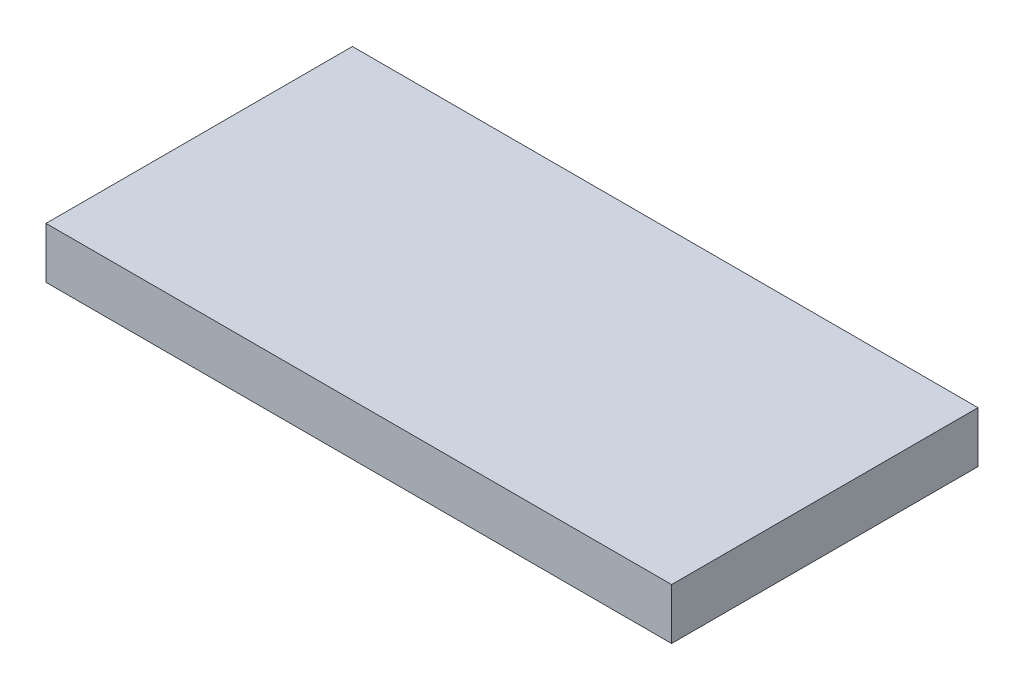
SolidWorks part; units mm, degrees
ref_plane "Front Plane" through (0, 0, 0) normal (0, 0, 1) x (1, 0, 0)
ref_plane "Top Plane" through (0, 0, 0) normal (0, 1, 0) x (1, 0, 0)
ref_plane "Right Plane" through (0, 0, 0) normal (1, 0, 0) x (0, 0, -1)
sketch "Sketch1" plane through (0, 0, 0) normal (0, 1, 0) x (1, 0, 0)
  line L1 (-49, -24) -> (49, -24)
  line L2 (-49, -24) -> (-49, 24)
  line L3 (-49, 24) -> (49, 24)
  line L4 (49, -24) -> (49, 24)
  line L5 (-49, -24) -> (49, 24) construction
  line L6 (-49, 24) -> (49, -24) construction
  point P0 (0, 0)
  dimension "D1" = 98
  dimension "D2" = 48
extrude "Boss-Extrude1" add sketch "Sketch1" along normal blind 8
